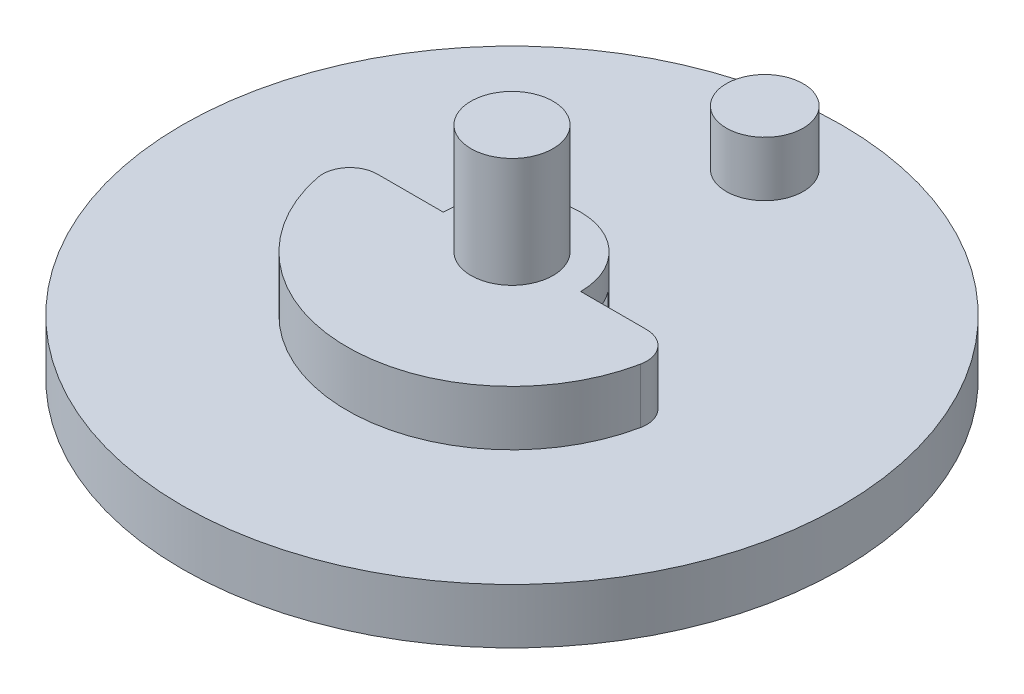
SolidWorks part; units mm, degrees
ref_plane "Front Plane" through (0, 0, 0) normal (0, 0, 1) x (1, 0, 0)
ref_plane "Top Plane" through (0, 0, 0) normal (0, 1, 0) x (1, 0, 0)
ref_plane "Right Plane" through (0, 0, 0) normal (1, 0, 0) x (0, 0, -1)
sketch "Sketch1" plane through (0, 0, 0) normal (0, 1, 0) x (1, 0, 0)
  circle A1 centre (0, 0) radius 12
extrude "Boss-Extrude1" add sketch "Sketch1" along normal blind 2
sketch "Sketch2" plane through (0, 2, 0) normal (0, 1, 0) x (1, 0, 0)
  line L0 (-6, 0) -> (6, 0)
  arc A1 (-6, 0) -> (6, 0) centre (0, 0) ccw
  circle A2 centre (0, 9.5) radius 1.5
extrude "Boss-Extrude2" add sketch "Sketch2" along normal blind 2
sketch "Sketch3" plane through (0, 0, 0) normal (0, -1, 0) x (1, 0, 0)
  circle A0 centre (0, 0) radius 1.5
extrude "Cut-Extrude1" cut sketch "Sketch3" against normal blind 5
sketch "Sketch4" plane through (0, 2, 0) normal (0, 1, 0) x (1, 0, 0)
  circle A0 centre (0, 0) radius 4
extrude "Cut-Extrude2" cut sketch "Sketch4" along normal up to surface (2 mm away) up to face at (0, 4, 1.875)
sketch "Sketch5" plane through (0, 2, 0) normal (0, 1, 0) x (1, 0, 0)
  circle A0 centre (0, 9.5) radius 1.5
extrude "Cut-Extrude3" cut sketch "Sketch5" along normal up to surface (2 mm away) up to face at (0, 4, -8)
sketch "Sketch6" plane through (0, 2, 0) normal (0, 1, 0) x (1, 0, 0)
  circle A0 centre (0, 9.2) radius 1.4
extrude "Boss-Extrude3" add sketch "Sketch6" along normal blind 2
sketch "Sketch7" plane through (0, 2, 0) normal (0, 1, 0) x (1, 0, 0)
  circle A0 centre (0, 0) radius 1.6
extrude "Cut-Extrude4" cut sketch "Sketch7" against normal blind 2
fillet "Fillet1" radius 1 2 edges at (6, 3, 0) (-6, 3, 0)
sketch "Sketch8" plane through (0, 0, 0) normal (0, -1, 0) x (-1, 0, 0)
  line L4 (0, -1.5) -> (-2, -1.5)
  line L7 (-2, -1.5) -> (2, -1.5)
  line L9 (2, 1.5) -> (-2, 1.5)
  circle A0 centre (0, 0) radius 4
  arc A3 (2, -1.5) -> (2, 1.5) centre (0, 0) ccw
  arc A4 (-2, 1.5) -> (-2, -1.5) centre (0, 0) ccw
  circle M1 centre (0, 0) radius 1.6
extrude "Boss-Extrude7" add sketch "Sketch8" along normal blind 5 contours A0 A4 L9 A3 L7 L4 M1
sketch "Sketch9" plane through (0, 2, 0) normal (0, 1, 0) x (1, 0, 0)
  circle A0 centre (0, 0) radius 1.6
extrude "Boss-Extrude8" add sketch "Sketch9" along normal blind 6 and the other way blind 2
sketch "Sketch10" plane through (0, 8, 0) normal (0, 1, 0) x (1, 0, 0)
  circle A0 centre (0, 0) radius 1.495
  circle A1 centre (0, 0) radius 1.6
extrude "Cut-Extrude5" cut sketch "Sketch10" against normal up to surface (6 mm away) up to face at (0, 2, 1.6)
sketch "Sketch11" plane through (0, 2, 0) normal (0, 1, 0) x (1, 0, 0)
  circle A0 centre (0, 0) radius 4
extrude "Boss-Extrude9" add sketch "Sketch11" along normal up to surface (2 mm away) up to face at (0, 4, 1.7892)
sketch "Sketch12" plane through (0, -5, 0) normal (0, -1, 0) x (-1, 0, 0)
  line L0 (2, -1.5) -> (0.5568, -1.5)
  line L1 (-0.5568, -1.5) -> (-2, -1.5)
  line L2 (-2, 1.5) -> (-0.5568, 1.5)
  line L3 (0.5568, 1.5) -> (2, 1.5)
  arc A0 (2, -1.5) -> (2, 1.5) centre (0, 0) ccw
  arc A1 (-2, -1.5) -> (-2, 1.5) centre (0, 0) cw
  arc A2 (0.5568, -1.5) -> (-0.5568, -1.5) centre (0, 0) cw
  arc A3 (0.5568, 1.5) -> (-0.5568, 1.5) centre (0, 0) ccw
extrude "Cut-Extrude6" cut sketch "Sketch12" against normal blind 8
sketch "Sketch13" plane through (0, -5, 0) normal (0, -1, 0) x (-1, 0, 0)
  circle A0 centre (0, 0) radius 6.8335
extrude "Cut-Extrude7" cut sketch "Sketch13" against normal blind 1
sketch "Sketch14" plane through (0, -4, 0) normal (0, -1, 0) x (-1, 0, 0)
  circle A0 centre (0, 0) radius 7.0331
extrude "Cut-Extrude8" cut sketch "Sketch14" against normal blind 1
sketch "Sketch15" plane through (0, -3, 0) normal (0, -1, 0) x (-1, 0, 0)
  circle A0 centre (0, 0) radius 8.7767
extrude "Cut-Extrude9" cut sketch "Sketch15" against normal blind 0.5
sketch "Sketch16" plane through (0, 4, 0) normal (0, 1, 0) x (1, 0, 0)
  line L0 (-4, 0) -> (-3, 0)
  line L1 (3, 0) -> (4, 0)
  line L2 (4, 0) -> (6.4884, 5.448)
  line L3 (6.4884, 5.448) -> (-6.4118, 6.0167)
  line L4 (-6.4118, 6.0167) -> (-4, 0)
  arc A0 (3, 0) -> (-3, 0) centre (0, 0) ccw
extrude "Cut-Extrude10" cut sketch "Sketch16" against normal up to surface (2 mm away) up to face at (0, 2, 12)
sketch "Sketch17" plane through (0, 4, 0) normal (0, 1, 0) x (1, 0, 0)
  line L0 (-3, 0) -> (-2.5, 0)
  line L1 (4.899, 0) -> (3, 0) construction
  line L2 (3, 0) -> (3.6951, 4.2614)
  line L3 (3.6951, 4.2614) -> (-7.0809, 5.4994)
  line L4 (-7.0809, 5.4994) -> (-3, 0)
  line L5 (2.5, 0) -> (3, 0)
  arc A0 (2.5, 0) -> (-2.5, 0) centre (0, 0) ccw
  arc A1 (3, 0) -> (-3, 0) centre (0, 0) ccw construction
extrude "Cut-Extrude11" cut sketch "Sketch17" against normal up to surface (2 mm away) up to face at (0, 2, 0.6225)
